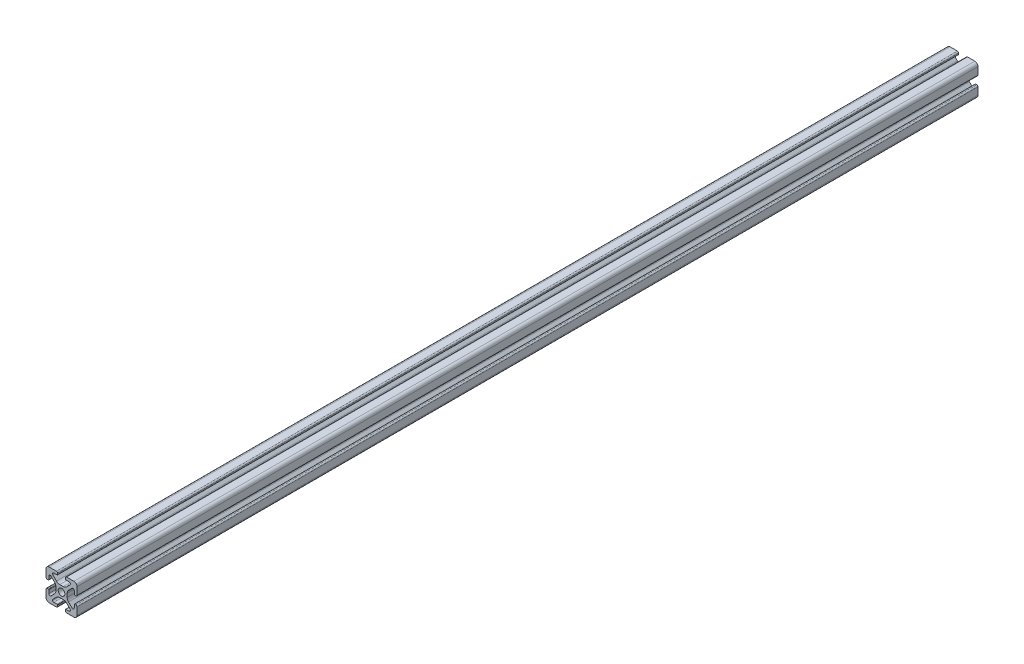
SolidWorks part; units mm, degrees
material "6061-T6 (SS)"
ref_plane "Front Plane" through (0, 0, 0) normal (0, 0, 1) x (1, 0, 0)
ref_plane "Top Plane" through (0, 0, 0) normal (0, 1, 0) x (1, 0, 0)
ref_plane "Right Plane" through (0, 0, 0) normal (1, 0, 0) x (0, 0, -1)
sketch "Sketch1" plane through (0, 0, 0) normal (0, 0, 1) x (1, 0, 0)
  line L2 (-9.9949, 7.9883) -> (-9.9949, 3.2893)
  line L3 (-7.9883, 9.9949) -> (-3.2893, 9.9949)
  line L4 (-2.5019, 9.2075) -> (-2.5019, 8.4963)
  line L5 (-2.8067, 8.1915) -> (-4.9149, 8.1915)
  line L6 (-5.5076, 6.7606) -> (-3.2528, 4.5058)
  line L7 (-6.7606, 5.5076) -> (-4.5058, 3.2528)
  line L8 (-8.1915, 4.9149) -> (-8.1915, 2.8067)
  line L9 (-8.4963, 2.5019) -> (-9.2075, 2.5019)
  line L11 (-1.1334, 3.6279) -> (1.1334, 3.6279)
  line L12 (-3.6279, 1.1334) -> (-3.6279, -1.1334)
  line L13 (8.4963, 2.5019) -> (9.2075, 2.5019)
  line L14 (8.1915, 4.9149) -> (8.1915, 2.8067)
  line L15 (9.9949, 7.9883) -> (9.9949, 3.2893)
  line L16 (7.9883, 9.9949) -> (3.2893, 9.9949)
  line L17 (2.5019, 9.2075) -> (2.5019, 8.4963)
  line L18 (2.8067, 8.1915) -> (4.9149, 8.1915)
  line L19 (3.6279, 1.1334) -> (3.6279, -1.1334)
  line L20 (5.5076, 6.7606) -> (3.2528, 4.5058)
  line L21 (6.7606, 5.5076) -> (4.5058, 3.2528)
  line L22 (-8.4963, -2.5019) -> (-9.2075, -2.5019)
  line L23 (-8.1915, -4.9149) -> (-8.1915, -2.8067)
  line L24 (-6.7606, -5.5076) -> (-4.5058, -3.2528)
  line L25 (-5.5076, -6.7606) -> (-3.2528, -4.5058)
  line L26 (-2.8067, -8.1915) -> (-4.9149, -8.1915)
  line L27 (-2.5019, -9.2075) -> (-2.5019, -8.4963)
  line L28 (-7.9883, -9.9949) -> (-3.2893, -9.9949)
  line L29 (-9.9949, -7.9883) -> (-9.9949, -3.2893)
  line L30 (9.9949, -7.9883) -> (9.9949, -3.2893)
  line L31 (7.9883, -9.9949) -> (3.2893, -9.9949)
  line L32 (2.5019, -9.2075) -> (2.5019, -8.4963)
  line L33 (2.8067, -8.1915) -> (4.9149, -8.1915)
  line L34 (5.5076, -6.7606) -> (3.2528, -4.5058)
  line L35 (6.7606, -5.5076) -> (4.5058, -3.2528)
  line L36 (8.1915, -4.9149) -> (8.1915, -2.8067)
  line L37 (8.4963, -2.5019) -> (9.2075, -2.5019)
  line L38 (-1.1334, -3.6279) -> (1.1334, -3.6279)
  circle A0 centre (0, 0) radius 2.1463
  arc A1 (-9.9949, 7.9883) -> (-7.9883, 9.9949) centre (-7.9883, 7.9883) cw
  arc A2 (-6.7606, 5.5076) -> (-8.1915, 4.9149) centre (-7.3533, 4.9149) ccw
  arc A3 (-4.9149, 8.1915) -> (-5.5076, 6.7606) centre (-4.9149, 7.3533) ccw
  arc A4 (-3.2893, 9.9949) -> (-2.5019, 9.2075) centre (-3.2893, 9.2075) cw
  arc A5 (-9.9949, 3.2893) -> (-9.2075, 2.5019) centre (-9.2075, 3.2893) ccw
  arc A6 (-8.1915, 2.8067) -> (-8.4963, 2.5019) centre (-8.4963, 2.8067) cw
  arc A7 (-2.5019, 8.4963) -> (-2.8067, 8.1915) centre (-2.8067, 8.4963) cw
  arc A8 (-1.1334, 3.6279) -> (-3.2528, 4.5058) centre (-1.1334, 6.6251) cw
  arc A9 (-3.6279, 1.1334) -> (-4.5058, 3.2528) centre (-6.6251, 1.1334) ccw
  arc A10 (8.1915, 2.8067) -> (8.4963, 2.5019) centre (8.4963, 2.8067) ccw
  arc A11 (9.9949, 3.2893) -> (9.2075, 2.5019) centre (9.2075, 3.2893) cw
  arc A12 (9.9949, 7.9883) -> (7.9883, 9.9949) centre (7.9883, 7.9883) ccw
  arc A13 (3.2893, 9.9949) -> (2.5019, 9.2075) centre (3.2893, 9.2075) ccw
  arc A14 (2.5019, 8.4963) -> (2.8067, 8.1915) centre (2.8067, 8.4963) ccw
  arc A15 (1.1334, 3.6279) -> (3.2528, 4.5058) centre (1.1334, 6.6251) ccw
  arc A16 (3.6279, 1.1334) -> (4.5058, 3.2528) centre (6.6251, 1.1334) cw
  arc A17 (6.7606, 5.5076) -> (8.1915, 4.9149) centre (7.3533, 4.9149) cw
  arc A18 (4.9149, 8.1915) -> (5.5076, 6.7606) centre (4.9149, 7.3533) cw
  arc A19 (-3.6279, -1.1334) -> (-4.5058, -3.2528) centre (-6.6251, -1.1334) cw
  arc A20 (-1.1334, -3.6279) -> (-3.2528, -4.5058) centre (-1.1334, -6.6251) ccw
  arc A21 (-2.5019, -8.4963) -> (-2.8067, -8.1915) centre (-2.8067, -8.4963) ccw
  arc A22 (-8.1915, -2.8067) -> (-8.4963, -2.5019) centre (-8.4963, -2.8067) ccw
  arc A23 (-9.9949, -3.2893) -> (-9.2075, -2.5019) centre (-9.2075, -3.2893) cw
  arc A24 (-3.2893, -9.9949) -> (-2.5019, -9.2075) centre (-3.2893, -9.2075) ccw
  arc A25 (-4.9149, -8.1915) -> (-5.5076, -6.7606) centre (-4.9149, -7.3533) cw
  arc A26 (-6.7606, -5.5076) -> (-8.1915, -4.9149) centre (-7.3533, -4.9149) cw
  arc A27 (-9.9949, -7.9883) -> (-7.9883, -9.9949) centre (-7.9883, -7.9883) ccw
  arc A28 (9.9949, -7.9883) -> (7.9883, -9.9949) centre (7.9883, -7.9883) cw
  arc A29 (6.7606, -5.5076) -> (8.1915, -4.9149) centre (7.3533, -4.9149) ccw
  arc A30 (4.9149, -8.1915) -> (5.5076, -6.7606) centre (4.9149, -7.3533) ccw
  arc A31 (3.2893, -9.9949) -> (2.5019, -9.2075) centre (3.2893, -9.2075) cw
  arc A32 (9.9949, -3.2893) -> (9.2075, -2.5019) centre (9.2075, -3.2893) ccw
  arc A33 (8.1915, -2.8067) -> (8.4963, -2.5019) centre (8.4963, -2.8067) cw
  arc A34 (2.5019, -8.4963) -> (2.8067, -8.1915) centre (2.8067, -8.4963) cw
  arc A35 (1.1334, -3.6279) -> (3.2528, -4.5058) centre (1.1334, -6.6251) cw
  arc A36 (3.6279, -1.1334) -> (4.5058, -3.2528) centre (6.6251, -1.1334) ccw
extrude "Boss-Extrude1" add sketch "Sketch1" along normal mid plane 580
